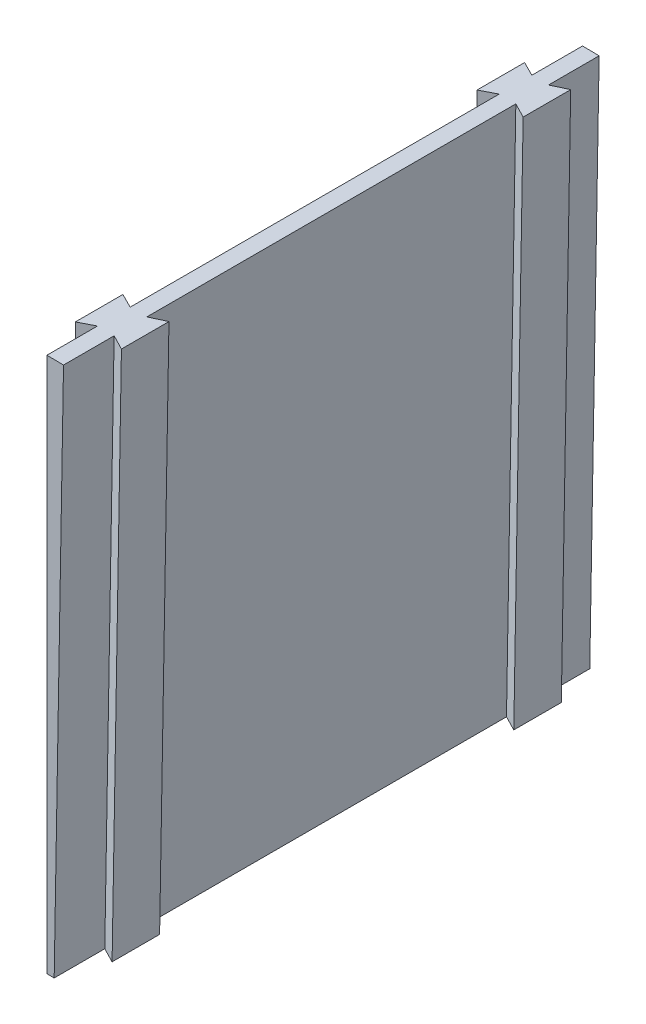
SolidWorks part; units mm, degrees
ref_plane "Front Plane" through (0, 0, 0) normal (0, 0, 1) x (1, 0, 0)
ref_plane "Top Plane" through (0, 0, 0) normal (0, 1, 0) x (1, 0, 0)
ref_plane "Right Plane" through (0, 0, 0) normal (1, 0, 0) x (0, 0, -1)
sketch "Sketch1" plane through (0, 0, 0) normal (0, 0, 1) x (1, 0, 0)
  line L0 (0, 79.375) -> (0, 180.975)
  line L1 (1.3853, 79.3629) -> (3.1584, 180.9474)
  circle A0 centre (0, 0) radius 79.375 construction
  circle A1 centre (0, 0) radius 180.975 construction
  arc A2 (0, 180.975) -> (3.1584, 180.9474) centre (0, 0) cw
  arc A3 (0, 79.375) -> (1.3853, 79.3629) centre (0, 0) cw
  dimension "D1" = 158.75
  dimension "D2" = 101.6
  dimension "D3" = 1
extrude "Boss-Extrude1" add sketch "Sketch1" along normal blind 101.6
ref_plane "Plane1" through (1.3853, 79.3629, 0) normal (-0.0175, -0.9998, 0) x (0, 0, -1)
sketch "Sketch2" plane through (1.3853, 79.3629, 0) normal (-0.0175, -0.9998, 0) x (0, 0, -1)
  line L10 (-92.0002, 0) -> (-93.4085, 2.794)
  line L15 (-101.6, 0) -> (0, 0) construction
  line L19 (-93.4085, 2.794) -> (-84.3915, 2.794)
  line L36 (-84.3915, 2.794) -> (-85.7998, 0)
  line L37 (-15.8002, 0) -> (-9.5998, 0)
  line L45 (-50.8, -1.3853) -> (-50.8, 25.7132) construction
  line L46 (-101.6, -1.3853) -> (0, -1.3853) construction
  line L55 (-85.7998, 0) -> (-92.0002, 0)
  line L56 (-17.2085, 2.794) -> (-15.8002, 0)
  line L57 (-8.1915, 2.794) -> (-17.2085, 2.794)
  line L58 (-9.5998, 0) -> (-8.1915, 2.794)
  point P4 (-88.9, 0)
  dimension "D1" = 63.25
  dimension "D2" = 9.017
  dimension "D3" = 2.794
  dimension "D4" = 12.7
extrude "Boss-Extrude2" add sketch "Sketch2" against normal up to surface (101.6 mm away)
ref_plane "Plane2" through (0, 79.375, 0) normal (0, -1, 0) x (0, 0, -1)
sketch "Sketch3" plane through (0, 79.375, 0) normal (0, -1, 0) x (0, 0, -1)
  line L0 (-92.0002, 0) -> (-93.4085, -2.7936)
  line L2 (-101.6, 0) -> (0, 0) construction
  line L13 (-93.4085, -2.7936) -> (-84.3915, -2.7936)
  line L14 (-84.3915, -2.7936) -> (-85.7998, 0)
  line L22 (-50.8, 0) -> (-50.8, 15.717) construction
  line L55 (-85.7998, 0) -> (-92.0002, 0)
  line L56 (-92.0002, 1.3853) -> (-85.7998, 1.3853) construction
  line L57 (-84.3915, 4.1789) -> (-93.4085, 4.1789) construction
  line L58 (-93.4085, 4.1789) -> (-92.0002, 1.3853) construction
  line L59 (-15.8002, 0) -> (-9.5998, 0)
  line L60 (-17.2085, -2.7936) -> (-15.8002, 0)
  line L61 (-8.1915, -2.7936) -> (-17.2085, -2.7936)
  line L62 (-9.5998, 0) -> (-8.1915, -2.7936)
  point P12 (-88.9, 1.3853)
  point P13 (-88.9, 0)
extrude "Boss-Extrude3" add sketch "Sketch3" against normal up to surface (101.5784 mm away)
